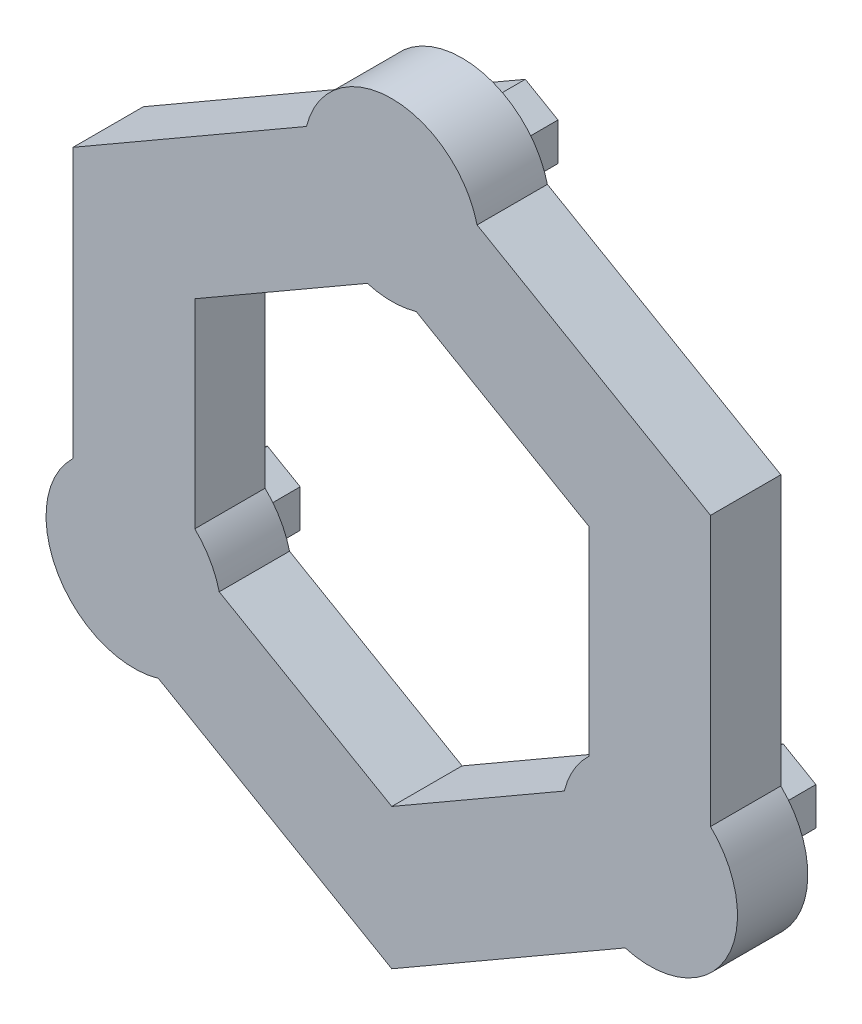
SolidWorks part; units mm, degrees
ref_plane "Front Plane" through (0, 0, 0) normal (0, 0, 1) x (1, 0, 0)
ref_plane "Top Plane" through (0, 0, 0) normal (0, 1, 0) x (1, 0, 0)
ref_plane "Right Plane" through (0, 0, 0) normal (1, 0, 0) x (0, 0, -1)
sketch "Sketch1" plane through (0, 0, 0) normal (0, 0, 1) x (1, 0, 0)
  line L0 (0, 21.1785) -> (0, 0) construction
  line L1 (0, 0) -> (18.3411, -10.5892) construction
  line L2 (0, 0) -> (-18.3411, -10.5892) construction
  line L3 (0, 21.1785) -> (0, 42.357) construction
  line L4 (0, -55) -> (0, 55) construction
  line L5 (18.3411, -10.5892) -> (36.6822, -21.1785) construction
  line L6 (-18.3411, -10.5892) -> (-36.6822, -21.1785) construction
  circle A0 centre (0, 0) radius 21.1785 construction
  circle A1 centre (0, 42.357) radius 21.1785 construction
  circle A2 centre (36.6822, -21.1785) radius 21.1785 construction
  circle A3 centre (-36.6822, -21.1785) radius 21.1785 construction
  dimension "D3" = 42.357
  dimension "D4" = 42.357
  dimension "D1" = 120
  dimension "D2" = 120
sketch "Sketch3" plane through (0, 0, 0) normal (0, 0, 1) x (1, 0, 0)
  line L0 (0, -55) -> (0, 55) construction
  line L1 (0, 42.357) -> (-36.6822, 21.1785) construction
  line L2 (-36.6822, 21.1785) -> (-36.6822, -21.1785) construction
  line L3 (-36.6822, -21.1785) -> (0, -42.357) construction
  line L4 (0, -42.357) -> (36.6822, -21.1785) construction
  line L5 (36.6822, -21.1785) -> (36.6822, 21.1785) construction
  line L6 (36.6822, 21.1785) -> (0, 42.357) construction
  line L7 (0, 32.357) -> (-28.022, 16.1785)
  line L8 (-28.022, 16.1785) -> (-28.022, -16.1785)
  line L9 (-28.022, -16.1785) -> (0, -32.357)
  line L10 (0, -32.357) -> (28.022, -16.1785)
  line L11 (28.022, -16.1785) -> (28.022, 16.1785)
  line L12 (28.022, 16.1785) -> (0, 32.357)
  line L13 (0, 52.357) -> (-45.3425, 26.1785)
  line L14 (-45.3425, 26.1785) -> (-45.3425, -26.1785)
  line L15 (-45.3425, -26.1785) -> (0, -52.357)
  line L16 (0, -52.357) -> (45.3425, -26.1785)
  line L17 (45.3425, -26.1785) -> (45.3425, 26.1785)
  line L18 (45.3425, 26.1785) -> (0, 52.357)
  line L19 (0, 21.1785) -> (0, 42.357) construction
  line L20 (-45.3425, 26.1785) -> (-28.022, 16.1785) construction
  circle A0 centre (0, 0) radius 36.6822 construction
  circle A1 centre (0, 0) radius 28.022 construction
  circle A2 centre (0, 0) radius 45.3425 construction
  circle A3 centre (-36.6822, -21.1785) radius 12.5
  circle A4 centre (36.6822, -21.1785) radius 12.5
  circle A5 centre (0, 42.357) radius 12.5
  point P35 (-36.6822, 21.1785)
  dimension "D2" = 25
  dimension "D1" = 20
extrude "Boss-Extrude2" add sketch "Sketch3" along normal mid plane 10 contours A5 L7 L8 A3 L9 L10 A4 L11 L12 | L14 A3 L15 | L16 A4 L17 | L18 A5 L13
sketch "Sketch4" plane through (0, 0, -5) normal (0, 0, -1) x (-1, 0, 0)
  line L1 (-41.3322, -23.8632) -> (-36.6822, -26.5479)
  line L2 (-36.6822, -26.5479) -> (-32.0322, -23.8632)
  line L3 (-32.0322, -23.8632) -> (-32.0322, -18.4938)
  line L4 (-32.0322, -18.4938) -> (-36.6822, -15.8091)
  line L5 (-36.6822, -15.8091) -> (-41.3322, -18.4938)
  line L6 (-41.3322, -18.4938) -> (-41.3322, -23.8632)
  line L7 (41.3322, -23.8632) -> (41.3322, -18.4938)
  line L8 (41.3322, -18.4938) -> (36.6822, -15.8091)
  line L9 (36.6822, -15.8091) -> (32.0322, -18.4938)
  line L10 (32.0322, -18.4938) -> (32.0322, -23.8632)
  line L11 (32.0322, -23.8632) -> (36.6822, -26.5479)
  line L12 (36.6822, -26.5479) -> (41.3322, -23.8632)
  line L13 (0, 47.7264) -> (-4.65, 45.0417)
  line L14 (-4.65, 45.0417) -> (-4.65, 39.6723)
  line L15 (-4.65, 39.6723) -> (0, 36.9876)
  line L16 (0, 36.9876) -> (4.65, 39.6723)
  line L17 (4.65, 39.6723) -> (4.65, 45.0417)
  line L18 (4.65, 45.0417) -> (0, 47.7264)
  circle A0 centre (-36.6822, -21.1785) radius 4.65 construction
  circle A1 centre (36.6822, -21.1785) radius 4.65 construction
  circle A2 centre (0, 42.357) radius 4.65 construction
  dimension "D1" = 9.3
extrude "Boss-Extrude3" add sketch "Sketch4" along normal blind 9
equation "\"sN\"= 12'Sun teeth"
equation "\"rN\"= 36'Ring teeth"
equation "\"pN\"= ( \"rN\" - \"sN\" ) / 2'Planet teeth"
equation "\"m\"= 3.5'Modulus"
equation "\"sRD\"= \"sN\" * \"m\"'Sun root diam"
equation "\"rRD\"= \"rN\" * \"m\"'Ring root diam"
equation "\"pRD\"= \"pN\" * \"m\"'Planet root diam"
equation "\"D3@Sketch1\"=\"sRD\"*\"sF\""
equation "\"D4@Sketch1\"=\"pRD\"*\"sF\""
equation "\"sF\"= 1.0085'Scale factor"
